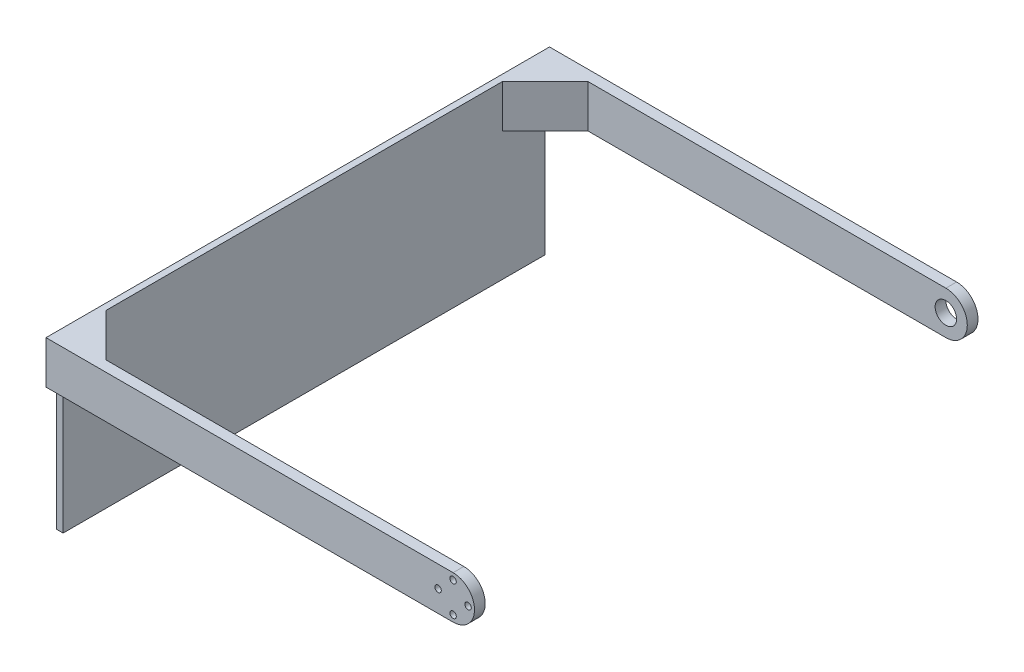
SolidWorks part; units mm, degrees
ref_plane "前视基准面" through (0, 0, 0) normal (0, 0, 1) x (1, 0, 0)
ref_plane "上视基准面" through (0, 0, 0) normal (0, 1, 0) x (1, 0, 0)
ref_plane "右视基准面" through (0, 0, 0) normal (1, 0, 0) x (0, 0, -1)
sketch "草图1" plane through (0, 0, 0) normal (0, 0, 1) x (1, 0, 0)
  line L0 (0, 0) -> (7, 0) construction
  line L1 (0, 10) -> (-190, 10)
  line L2 (-190, 10) -> (-190, -10)
  line L3 (-190, -10) -> (0, -10)
  arc A0 (0, -10) -> (0, 10) centre (0, 0) ccw
  circle A1 centre (7, 0) radius 1.5
  circle A2 centre (0, -7) radius 1.5
  circle A3 centre (-7, 0) radius 1.5
  circle A4 centre (0, 7) radius 1.5
  dimension "D1" = 20
  dimension "D2" = 3
  dimension "D3" = 7
  dimension "D5" = 7
  dimension "D6" = 190
  dimension "D4" = 4
extrude "凸台-拉伸1" add sketch "草图1" along normal blind 5
sketch "草图2" plane through (0, 0, 0) normal (0, 0, -1) x (-1, 0, 0)
  line L0 (190, 10) -> (190, -10)
  line L3 (190, -10) -> (0, -10) construction
  line L4 (187, -10) -> (187, 10)
  line L5 (0, 10) -> (190, 10) construction
  line L6 (187, 10) -> (190, 10)
  line L7 (188.5, -43.083) -> (188.5, 32.493) construction
  line L8 (187, -10) -> (187, -70)
  line L9 (187, -70) -> (190, -70)
  line L10 (190, -70) -> (190, -10)
  dimension "D1" = 1.5
  dimension "D2" = 60
extrude "凸台-拉伸2" add sketch "草图2" along normal blind 225
sketch "草图3" plane through (0, 10, 0) normal (0, 1, 0) x (1, 0, 0)
  line L0 (-187, 20) -> (-167, 0)
  line L1 (-187, 225) -> (-187, 0) construction
  line L2 (0, 0) -> (-187, 0) construction
  dimension "D1" = 20
  dimension "D2" = 20
rib "筋1" sketch "草图3" sketch "草图3" thickness 20 extrusion direction parallel to sketch draft on no parameters "D1"=20
ref_plane "基准面1" through (0, 0, -112.5) normal (0, 0, 1) x (1, 0, 0)
sketch "草图4" plane through (0, 0, -225) normal (0, 0, -1) x (-1, 0, 0)
  line L0 (190, -70) -> (190, 10) construction
  line L2 (190, -10) -> (190, 10)
  line L3 (0, -10) -> (167, -10)
  line L4 (167, -10) -> (167, 10)
  line L5 (167, 10) -> (0, 10)
  line L8 (190, 10) -> (0, 10)
  line L9 (0, -10) -> (190, -10)
  circle A0 centre (0, 0) radius 5
  arc A1 (0, 10) -> (0, -10) centre (0, 0) ccw
  arc A2 (0, 10) -> (0, -10) centre (0, 0) ccw
  point P4 (0, 0)
  dimension "D2" = 10
  dimension "D1" = 0
extrude "凸台-拉伸3" add sketch "草图4" along normal blind 5
mirror "镜向1" about plane through (0, 0, -112.5) normal (0, 0, 1) of "筋1"
